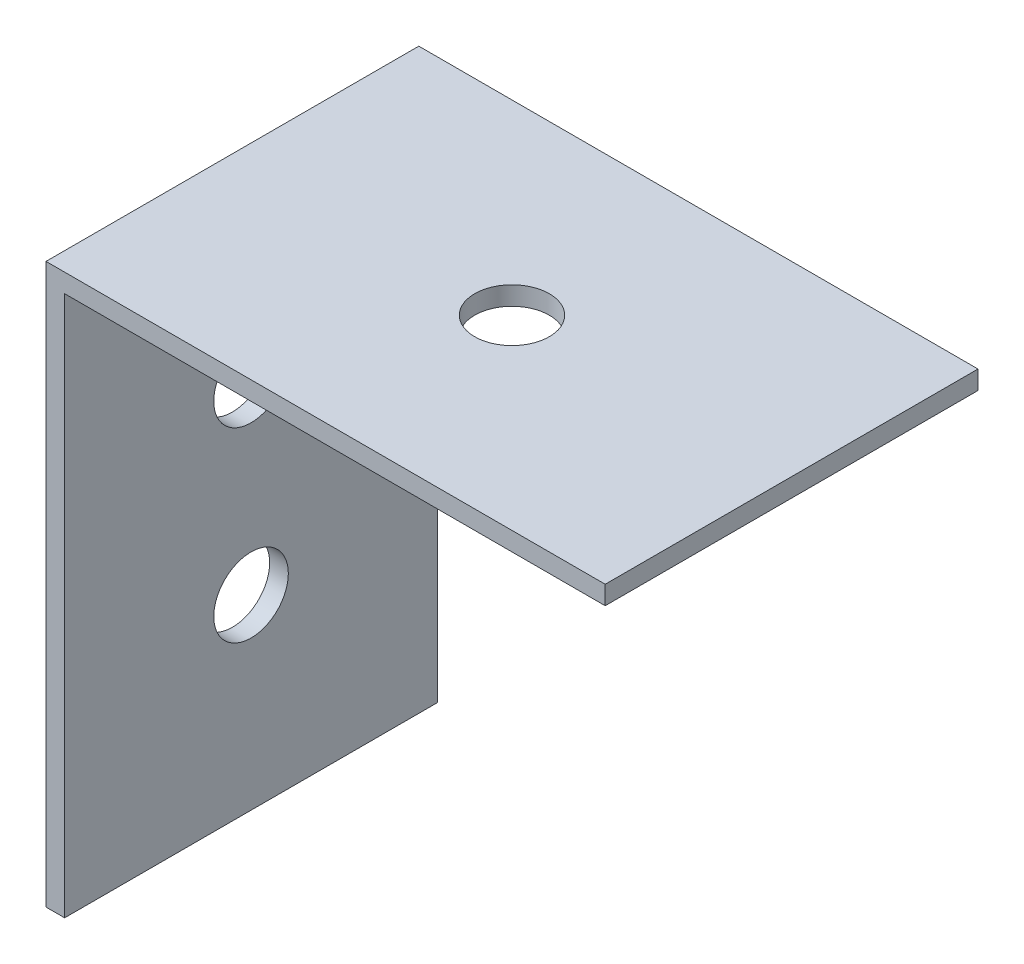
SolidWorks part; units mm, degrees
ref_plane "Front Plane" through (0, 0, 0) normal (0, 0, 1) x (1, 0, 0)
ref_plane "Top Plane" through (0, 0, 0) normal (0, 1, 0) x (1, 0, 0)
ref_plane "Right Plane" through (0, 0, 0) normal (1, 0, 0) x (0, 0, -1)
sketch "Sketch2" plane through (0, 0, 0) normal (1, 0, 0) x (0, 0, -1)
  line L1 (0, 0) -> (20, 0)
  line L2 (0, 0) -> (0, 30)
  line L3 (0, 30) -> (20, 30)
  line L4 (20, 0) -> (20, 30)
  circle A0 centre (10, 20) radius 2
  circle A1 centre (10, 10) radius 2
  dimension "D3" = 4
  dimension "D4" = 4
  dimension "D1" = 20
  dimension "D2" = 30
  dimension "D5" = 10
  dimension "D6" = 10
  dimension "D7" = 10
  dimension "D8" = 10
extrude "Boss-Extrude1" add sketch "Sketch2" along normal blind 1
sketch "Sketch3" plane through (1, 0, 0) normal (1, 0, 0) x (0, 0, -1)
  line L0 (20, 0) -> (20, 30) construction
  line L1 (0, 30) -> (20, 30)
  line L2 (0, 30) -> (0, 29)
  line L3 (0, 29) -> (20, 29)
  line L4 (20, 30) -> (20, 29)
  dimension "D1" = 1
extrude "Boss-Extrude2" add sketch "Sketch3" along normal blind 29
sketch "Sketch4" plane through (0, 30, 0) normal (0, 1, 0) x (1, 0, 0)
  line L0 (30, 20) -> (0, 20) construction
  line L1 (30, 20) -> (30, 0) construction
  circle A0 centre (15, 10) radius 2
  dimension "D3" = 4
  dimension "D1" = 10
  dimension "D2" = 15
extrude "Cut-Extrude1" cut sketch "Sketch4" against normal blind 30
